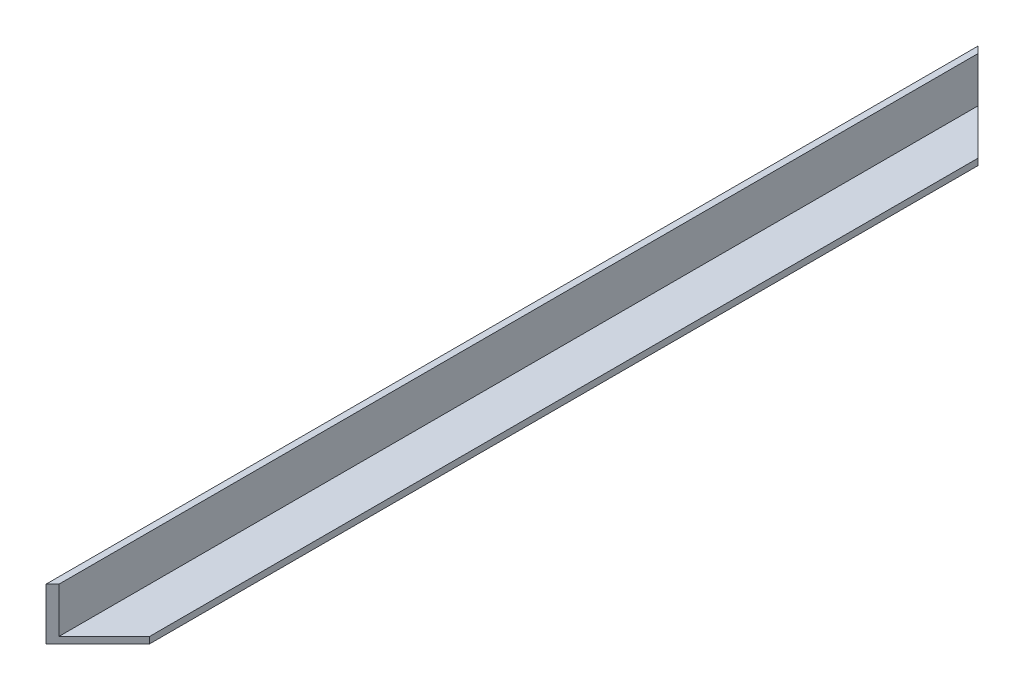
SolidWorks part; units mm, degrees
ref_plane "Front Plane" through (0, 0, 0) normal (0, 0, 1) x (1, 0, 0)
ref_plane "Top Plane" through (0, 0, 0) normal (0, 1, 0) x (1, 0, 0)
ref_plane "Right Plane" through (0, 0, 0) normal (1, 0, 0) x (0, 0, -1)
sketch "Sketch1" plane through (0, 0, 0) normal (0, 0, 1) x (1, 0, 0)
  line L0 (0, 0) -> (25.4, 0)
  line L1 (55, 0) -> (-55, 0) construction
  line L2 (25.4, 0) -> (25.4, 3.175)
  line L3 (25.4, 3.175) -> (3.175, 3.175)
  line L4 (3.175, 3.175) -> (3.175, 25.4)
  line L5 (3.175, 25.4) -> (0, 25.4)
  line L6 (0, -55) -> (0, 55) construction
  line L7 (0, 25.4) -> (0, 0)
  dimension "D1" = 25.4
  dimension "D2" = 25.4
  dimension "D3" = 3.175
  dimension "D4" = 3.175
extrude "Boss-Extrude1" add sketch "Sketch1" along normal blind 457.2
sketch "Sketch2" plane through (0, 3.175, 0) normal (0, 1, 0) x (1, 0, 0)
  line L0 (0, 0) -> (25.4, -25.4)
  line L1 (25.4, -457.2) -> (25.4, 0) construction
  line L2 (25.4, -25.4) -> (25.4, 0)
  line L3 (-13.97, 0) -> (13.97, 0) construction
  line L4 (25.4, 0) -> (0, 0)
  line L5 (0, -457.2) -> (25.4, -431.8)
  line L6 (0, -13.97) -> (0, 13.97) construction
  line L7 (25.4, -431.8) -> (25.4, -457.2)
  line L8 (25.4, -457.2) -> (0, -457.2)
  dimension "D1" = 45
  dimension "D2" = 45
extrude "Cut-Extrude1" cut sketch "Sketch2" against normal through all both and the other way through all
